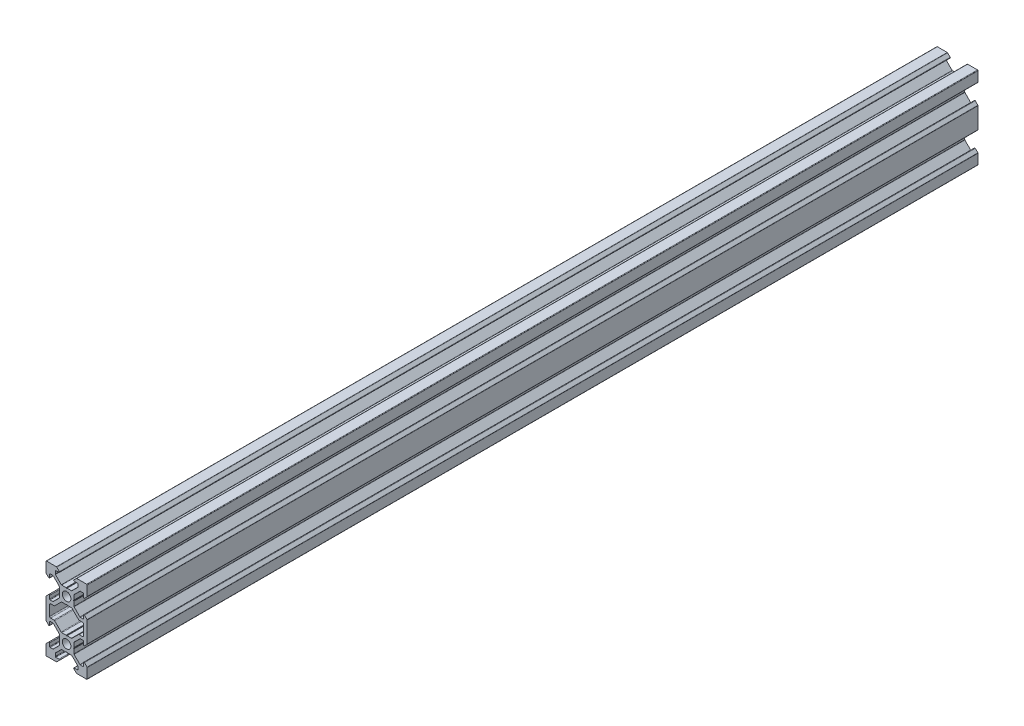
SolidWorks part; units mm, degrees
ref_plane "Front Plane" through (0, 0, 0) normal (0, 0, 1) x (1, 0, 0)
ref_plane "Top Plane" through (0, 0, 0) normal (0, 1, 0) x (1, 0, 0)
ref_plane "Right Plane" through (0, 0, 0) normal (1, 0, 0) x (0, 0, -1)
sketch "Sketch1" plane through (0, 0, 0) normal (0, 0, 1) x (1, 0, 0)
  line L0 (3.5607, 3.5607) -> (10.6317, 10.6317) construction
  line L1 (2.5, -3.5607) -> (-2.5, -3.5607)
  line L2 (3.5607, -2.5) -> (3.5607, 2.5)
  line L3 (2.5, 3.5607) -> (-2.5, 3.5607)
  line L4 (-3.5607, -2.5) -> (-3.5607, 2.5)
  line L5 (3.5607, -3.5607) -> (-3.5607, 3.5607) construction
  line L6 (3.5607, 3.5607) -> (-3.5607, -3.5607) construction
  line L7 (2.5, 3.5607) -> (5.5, 6.5607)
  line L8 (5.5, 6.5607) -> (5.5, 8.2521)
  line L9 (5.5, 8.2521) -> (3.1, 8.2521)
  line L10 (3.1, 8.2521) -> (4.8479, 10)
  line L11 (4.8479, 10) -> (10, 10)
  line L12 (3.5607, 2.5) -> (6.5607, 5.5)
  line L13 (6.5607, 5.5) -> (8.2521, 5.5)
  line L14 (8.2521, 5.5) -> (8.2521, 3.1)
  line L15 (8.2521, 3.1) -> (10, 4.8479)
  line L16 (10, 4.8479) -> (10, 10)
  line L17 (0, -55) -> (0, 55) construction
  line L18 (-3.5607, 3.5607) -> (-10.6317, 10.6317) construction
  line L19 (-10, 4.8479) -> (-10, 10)
  line L20 (-8.2521, 3.1) -> (-10, 4.8479)
  line L21 (-8.2521, 5.5) -> (-8.2521, 3.1)
  line L22 (-6.5607, 5.5) -> (-8.2521, 5.5)
  line L23 (-3.5607, 2.5) -> (-6.5607, 5.5)
  line L24 (-4.8479, 10) -> (-10, 10)
  line L25 (-3.1, 8.2521) -> (-4.8479, 10)
  line L26 (-5.5, 8.2521) -> (-3.1, 8.2521)
  line L27 (-5.5, 6.5607) -> (-5.5, 8.2521)
  line L28 (-2.5, 3.5607) -> (-5.5, 6.5607)
  line L29 (-8.2521, -7) -> (-5.9393, -7)
  line L30 (55, 0) -> (-55, 0) construction
  line L31 (-3.5607, -3.5607) -> (-10.6317, -10.6317) construction
  line L32 (3.5607, -3.5607) -> (10.6317, -10.6317) construction
  line L33 (-2.5, -3.5607) -> (-5.5, -6.5607)
  line L34 (-5.5, -6.5607) -> (-5.9393, -7)
  line L35 (5.5, -6.5607) -> (5.9393, -7)
  line L36 (8.2521, -7) -> (5.9393, -7)
  line L37 (-12.2633, -10) -> (14.5346, -10) construction
  line L38 (-3.5607, -2.5) -> (-6.5607, -5.5)
  line L39 (-6.5607, -5.5) -> (-8.2521, -5.5)
  line L40 (-8.2521, -5.5) -> (-8.2521, -3.1)
  line L41 (-8.2521, -3.1) -> (-10, -4.8479)
  line L42 (-10, -4.8479) -> (-10, -7)
  line L43 (10, -4.8479) -> (10, -7)
  line L44 (8.2521, -3.1) -> (10, -4.8479)
  line L45 (8.2521, -5.5) -> (8.2521, -3.1)
  line L46 (6.5607, -5.5) -> (8.2521, -5.5)
  line L47 (3.5607, -2.5) -> (6.5607, -5.5)
  line L48 (-3.5607, -23.5607) -> (-10.6317, -30.6317) construction
  line L49 (3.5607, -23.5607) -> (-3.5607, -16.4393) construction
  line L50 (3.5607, -16.4393) -> (-3.5607, -23.5607) construction
  line L51 (3.5607, -23.5607) -> (10.6317, -30.6317) construction
  line L52 (2.5, -3.5607) -> (5.5, -6.5607)
  line L53 (2.5, -16.4393) -> (5.5, -13.4393)
  line L54 (3.5607, -17.5) -> (6.5607, -14.5)
  line L55 (6.5607, -14.5) -> (8.2521, -14.5)
  line L56 (8.2521, -14.5) -> (8.2521, -16.9)
  line L57 (8.2521, -16.9) -> (10, -15.1521)
  line L58 (10, -15.1521) -> (10, -13)
  line L59 (-10, -15.1521) -> (-10, -13)
  line L60 (-8.2521, -16.9) -> (-10, -15.1521)
  line L61 (-8.2521, -14.5) -> (-8.2521, -16.9)
  line L62 (-6.5607, -14.5) -> (-8.2521, -14.5)
  line L63 (-3.5607, -17.5) -> (-6.5607, -14.5)
  line L64 (8.2521, -13) -> (5.9393, -13)
  line L65 (5.5, -13.4393) -> (5.9393, -13)
  line L66 (-5.5, -13.4393) -> (-5.9393, -13)
  line L67 (-2.5, -16.4393) -> (-5.5, -13.4393)
  line L68 (-8.2521, -13) -> (-5.9393, -13)
  line L69 (-2.5, -23.5607) -> (-5.5, -26.5607)
  line L70 (-5.5, -26.5607) -> (-5.5, -28.2521)
  line L71 (-5.5, -28.2521) -> (-3.1, -28.2521)
  line L72 (-3.1, -28.2521) -> (-4.8479, -30)
  line L73 (-4.8479, -30) -> (-10, -30)
  line L74 (-3.5607, -22.5) -> (-6.5607, -25.5)
  line L75 (-6.5607, -25.5) -> (-8.2521, -25.5)
  line L76 (-8.2521, -25.5) -> (-8.2521, -23.1)
  line L77 (-8.2521, -23.1) -> (-10, -24.8479)
  line L78 (-10, -24.8479) -> (-10, -30)
  line L79 (10, -24.8479) -> (10, -30)
  line L80 (8.2521, -23.1) -> (10, -24.8479)
  line L81 (8.2521, -25.5) -> (8.2521, -23.1)
  line L82 (6.5607, -25.5) -> (8.2521, -25.5)
  line L83 (3.5607, -22.5) -> (6.5607, -25.5)
  line L84 (4.8479, -30) -> (10, -30)
  line L85 (3.1, -28.2521) -> (4.8479, -30)
  line L86 (5.5, -28.2521) -> (3.1, -28.2521)
  line L87 (5.5, -26.5607) -> (5.5, -28.2521)
  line L88 (2.5, -23.5607) -> (5.5, -26.5607)
  line L89 (-3.5607, -17.5) -> (-3.5607, -22.5)
  line L90 (2.5, -23.5607) -> (-2.5, -23.5607)
  line L91 (3.5607, -17.5) -> (3.5607, -22.5)
  line L92 (2.5, -16.4393) -> (-2.5, -16.4393)
  line L93 (-10, -7) -> (-10, -13)
  line L94 (-8.2521, -13) -> (-8.2521, -7)
  line L95 (8.2521, -13) -> (8.2521, -7)
  line L96 (10, -7) -> (10, -13)
  circle A0 centre (0, 0) radius 2.1
  circle A1 centre (0, -20) radius 2.1
  point P0 (0, 0)
  point P102 (0, -20)
  dimension "D10" = 4.2
  dimension "D11" = 4.2
  dimension "D1" = 1.5
  dimension "D2" = 10
  dimension "D3" = 20
  dimension "D4" = 6.2
  dimension "D5" = 11
  dimension "D6" = 45
  dimension "D7" = 1.5
  dimension "D8" = 10
  dimension "D9" = 5
extrude "Boss-Extrude1" add sketch "Sketch1" along normal blind 432.69
fillet "Fillet1" radius 0.25 64 edges at (5.5, 6.5607, 216.345) (5.5, 8.2521, 216.345) (3.1, 8.2521, 216.345) (4.8479, 10, 216.345) (10, 10, 216.345) (10, 4.8479, 216.345) (8.2521, 3.1, 216.345) (8.2521, 5.5, 216.345) (6.5607, 5.5, 216.345) (3.5607, 2.5, 216.345) (3.5607, -2.5, 216.345) (6.5607, -5.5, 216.345) (8.2521, -5.5, 216.345) (8.2521, -3.1, 216.345) (10, -4.8479, 216.345) (10, -15.1521, 216.345) (8.2521, -16.9, 216.345) (8.2521, -14.5, 216.345) (6.5607, -14.5, 216.345) (3.5607, -17.5, 216.345) (3.5607, -22.5, 216.345) (6.5607, -25.5, 216.345) (8.2521, -25.5, 216.345) (8.2521, -23.1, 216.345) (10, -24.8479, 216.345) (10, -30, 216.345) (4.8479, -30, 216.345) (3.1, -28.2521, 216.345) (5.5, -28.2521, 216.345) (5.5, -26.5607, 216.345) (2.5, -23.5607, 216.345) (-2.5, -23.5607, 216.345) (-5.5, -26.5607, 216.345) (-5.5, -28.2521, 216.345) (-3.1, -28.2521, 216.345) (-4.8479, -30, 216.345) (-10, -30, 216.345) (-10, -24.8479, 216.345) (-8.2521, -23.1, 216.345) (-8.2521, -25.5, 216.345) (-6.5607, -25.5, 216.345) (-3.5607, -22.5, 216.345) (-3.5607, -17.5, 216.345) (-6.5607, -14.5, 216.345) (-8.2521, -14.5, 216.345) (-8.2521, -16.9, 216.345) (-10, -15.1521, 216.345) (-10, -4.8479, 216.345) (-8.2521, -3.1, 216.345) (-8.2521, -5.5, 216.345) (-6.5607, -5.5, 216.345) (-3.5607, -2.5, 216.345) (-3.5607, 2.5, 216.345) (-6.5607, 5.5, 216.345) (-8.2521, 5.5, 216.345) (-8.2521, 3.1, 216.345) (-10, 4.8479, 216.345) (-10, 10, 216.345) (-4.8479, 10, 216.345) (-5.5, 8.2521, 216.345) (-5.5, 6.5607, 216.345) (-2.5, 3.5607, 216.345) (2.5, 3.5607, 216.345) (-3.1, 8.2521, 216.345)
fillet "Fillet2" radius 0.5 12 edges at (-5.9393, -7, 216.345) (-8.2521, -7, 216.345) (-8.2521, -13, 216.345) (-5.9393, -13, 216.345) (-2.5, -16.4393, 216.345) (2.5, -16.4393, 216.345) (8.2521, -7, 216.345) (5.9393, -7, 216.345) (2.5, -3.5607, 216.345) (-2.5, -3.5607, 216.345) (5.9393, -13, 216.345) (8.2521, -13, 216.345)
sketch "Sketch2" plane through (0, 0, 432.69) normal (0, 0, 1) x (1, 0, 0)
  line L4 (0, 3.5607) -> (0, 3.1447) construction
  line L5 (2.3964, 3.5607) -> (-2.3964, 3.5607) construction
  line L6 (0, 3.399) -> (-0.2423, 3.5607)
  line L7 (0, 3.399) -> (0.2423, 3.5607)
  line L8 (-0.2423, 3.5607) -> (0.2423, 3.5607)
  line L9 (55, 0) -> (-55, 0) construction
  line L10 (0, -3.5607) -> (0, -3.1447) construction
  line L11 (0, -3.399) -> (0.2423, -3.5607)
  line L12 (0, -3.399) -> (-0.2423, -3.5607)
  line L13 (-0.2423, -3.5607) -> (0.2423, -3.5607)
  line L14 (0, 0) -> (-4.0856, 4.0856) construction
  line L15 (-8.2521, -10) -> (4.1581, -10) construction
  line L16 (-8.2521, -7.5) -> (-8.2521, -12.5) construction
  line L17 (3.5607, 0) -> (3.1447, 0) construction
  line L18 (3.5607, 0.2423) -> (3.5607, -0.2423)
  line L19 (3.399, 0) -> (3.5607, 0.2423)
  line L20 (3.399, 0) -> (3.5607, -0.2423)
  line L21 (-3.5607, 0) -> (-3.1447, 0) construction
  line L22 (-3.5607, 0.2423) -> (-3.5607, -0.2423)
  line L23 (-3.399, 0) -> (-3.5607, -0.2423)
  line L24 (-3.399, 0) -> (-3.5607, 0.2423)
  line L25 (-3.5607, -20) -> (-3.1447, -20) construction
  line L26 (3.5607, -20) -> (3.1447, -20) construction
  line L27 (0, -20) -> (-4.0856, -24.0856) construction
  line L28 (0, -16.4393) -> (0, -16.8553) construction
  line L29 (0, -23.5607) -> (0, -23.1447) construction
  line L30 (-3.399, -20) -> (-3.5607, -20.2423)
  line L31 (-3.399, -20) -> (-3.5607, -19.7577)
  line L32 (-3.5607, -20.2423) -> (-3.5607, -19.7577)
  line L33 (3.399, -20) -> (3.5607, -19.7577)
  line L34 (3.399, -20) -> (3.5607, -20.2423)
  line L35 (3.5607, -20.2423) -> (3.5607, -19.7577)
  line L36 (-0.2423, -16.4393) -> (0.2423, -16.4393)
  line L37 (0, -16.601) -> (-0.2423, -16.4393)
  line L38 (0, -16.601) -> (0.2423, -16.4393)
  line L39 (-0.2423, -23.5607) -> (0.2423, -23.5607)
  line L40 (0, -23.399) -> (0.2423, -23.5607)
  line L41 (0, -23.399) -> (-0.2423, -23.5607)
extrude "Cut-Extrude1" cut sketch "Sketch2" against normal through all
